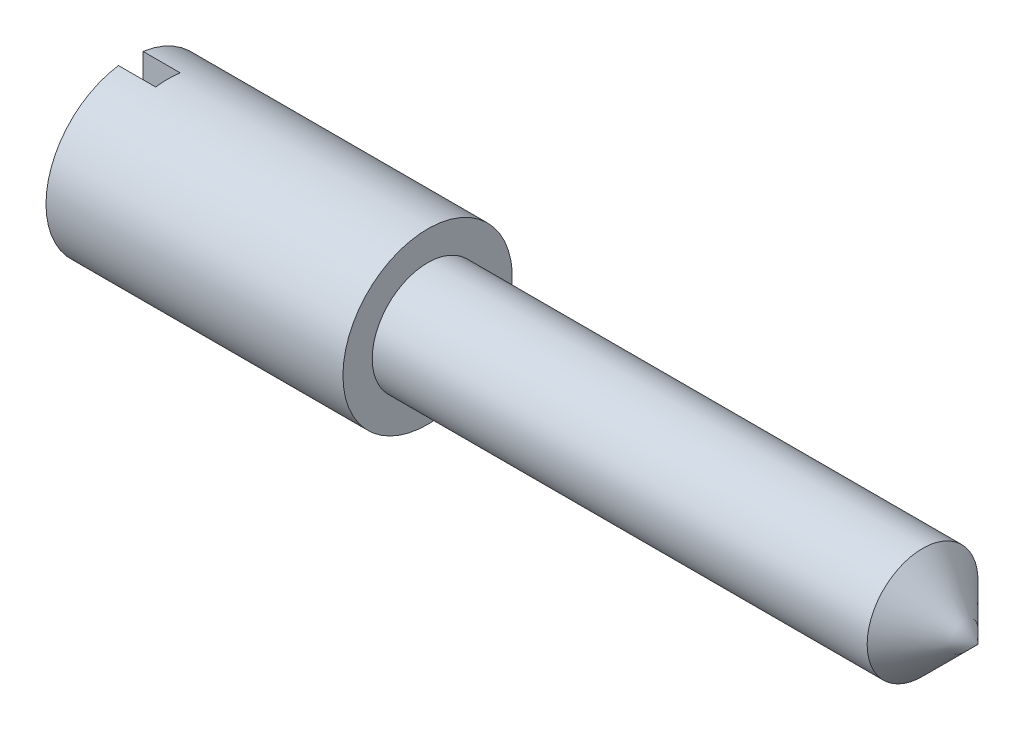
SolidWorks part; units mm, degrees
ref_plane "Front Plane" through (0, 0, 0) normal (0, 0, 1) x (1, 0, 0)
ref_plane "Top Plane" through (0, 0, 0) normal (0, 1, 0) x (1, 0, 0)
ref_plane "Right Plane" through (0, 0, 0) normal (1, 0, 0) x (0, 0, -1)
sketch "Sketch2" plane through (0, 0, 0) normal (0, 1, 0) x (1, 0, 0)
  line L0 (0, 0) -> (15.875, 0)
  line L1 (0, 0) -> (0, 0.9398)
  line L2 (0, 0.9398) -> (-9.525, 0.9398)
  line L3 (-9.525, 0.9398) -> (-9.525, -1.778)
  line L4 (-9.525, -1.778) -> (17.653, -1.778)
  line L5 (15.875, 0) -> (17.653, -1.778)
  dimension "D1" = 15.875
  dimension "D2" = 9.525
  dimension "D3" = 1.778
  dimension "D4" = 2.7178
  dimension "D5" = 27.178
revolve "Revolve1" add sketch "Sketch2" angle 360 about L4
sketch "Sketch3" plane through (-9.525, 0, 0) normal (-1, 0, 0) x (0, 0, 1)
  line L0 (1.778, 2.7178) -> (1.778, -2.7178) construction
  line L1 (2.1717, 2.7178) -> (1.3843, 2.7178)
  line L2 (1.3843, 2.7178) -> (1.3843, -2.7178)
  line L3 (1.3843, -2.7178) -> (2.1717, -2.7178)
  line L4 (2.1717, -2.7178) -> (2.1717, 2.7178)
  circle A0 centre (1.778, 0) radius 2.7178 construction
  point P8 (1.778, 2.7178)
  dimension "D1" = 0.7874
extrude "Cut-Extrude1" cut sketch "Sketch3" against normal blind 1.1938
